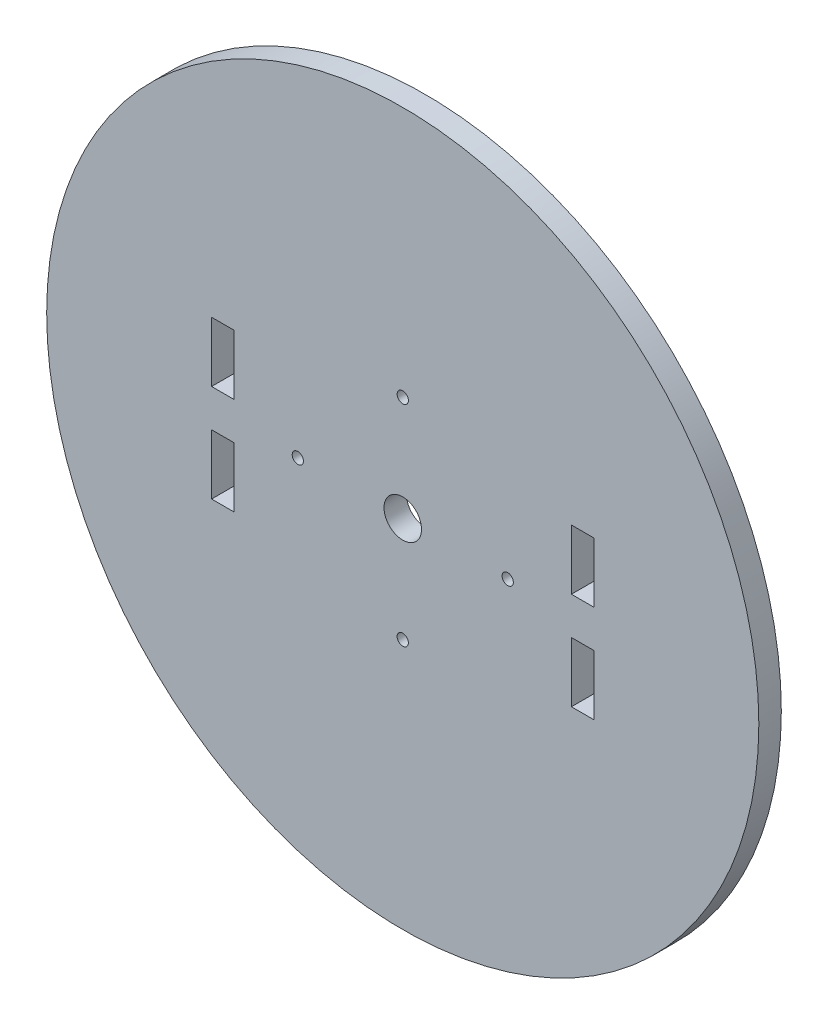
SolidWorks part; units mm, degrees
ref_plane "Alzado" through (0, 0, 0) normal (0, 0, 1) x (1, 0, 0)
ref_plane "Planta" through (0, 0, 0) normal (0, 1, 0) x (1, 0, 0)
ref_plane "Vista lateral" through (0, 0, 0) normal (1, 0, 0) x (0, 0, -1)
sketch "Croquis1" plane through (0, 0, 0) normal (0, 0, 1) x (1, 0, 0)
  circle A0 centre (0, 0) radius 47.5
  circle A1 centre (0, 0) radius 2.5
  circle A2 centre (0, -14) radius 0.75
  circle A3 centre (0, 0) radius 14 construction
  circle A4 centre (-14, 0) radius 0.75
  circle A5 centre (0, 0) radius 14 construction
  circle A6 centre (0, 14) radius 0.75
  circle A7 centre (0, 0) radius 14 construction
  circle A8 centre (14, 0) radius 0.75
  circle A9 centre (0, 0) radius 14 construction
  point P19 (0, 0)
  dimension "D1" = 95
  dimension "D2" = 5
  dimension "D3" = 28
  dimension "D4" = 1.5
  dimension "D5" = 4
extrude "Saliente-Extruir1" add sketch "Croquis1" along normal blind 3
sketch "Croquis2" plane through (0, 0, 3) normal (0, 0, 1) x (1, 0, 0)
  line L0 (24, 2.5) -> (24, -2.5) construction
  line L1 (22.5, 10.5) -> (25.5, 10.5)
  line L2 (22.5, 10.5) -> (22.5, 2.5)
  line L3 (22.5, 2.5) -> (25.5, 2.5)
  line L4 (25.5, 10.5) -> (25.5, 2.5)
  line L5 (22.5, -2.5) -> (25.5, -2.5)
  line L6 (22.5, -2.5) -> (22.5, -10.5)
  line L7 (22.5, -10.5) -> (25.5, -10.5)
  line L8 (25.5, -2.5) -> (25.5, -10.5)
  line L9 (0, 0) -> (0, -47.5) construction
  line L10 (-24, 2.5) -> (-24, -2.5) construction
  line L11 (-25.5, -2.5) -> (-25.5, -10.5)
  line L12 (-22.5, -10.5) -> (-25.5, -10.5)
  line L13 (-22.5, -2.5) -> (-22.5, -10.5)
  line L14 (-22.5, -2.5) -> (-25.5, -2.5)
  line L15 (-25.5, 10.5) -> (-25.5, 2.5)
  line L16 (-22.5, 2.5) -> (-25.5, 2.5)
  line L17 (-22.5, 10.5) -> (-22.5, 2.5)
  line L18 (-22.5, 10.5) -> (-25.5, 10.5)
  circle A0 centre (0, 0) radius 47.5 construction
  point P10 (24, 0)
  dimension "D1" = 3
  dimension "D2" = 5
  dimension "D3" = 8
  dimension "D4" = 24
extrude "Cortar-Extruir1" cut sketch "Croquis2" against normal through all
